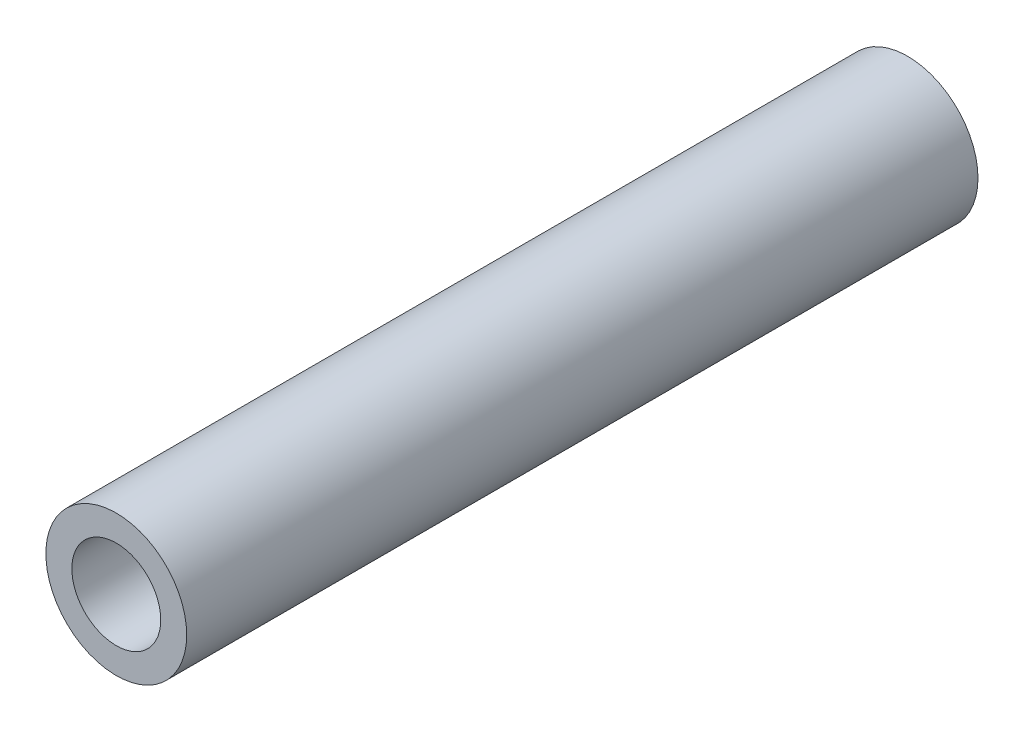
SolidWorks part; units mm, degrees
ref_plane "Front Plane" through (0, 0, 0) normal (0, 0, 1) x (1, 0, 0)
ref_plane "Top Plane" through (0, 0, 0) normal (0, 1, 0) x (1, 0, 0)
ref_plane "Right Plane" through (0, 0, 0) normal (1, 0, 0) x (0, 0, -1)
sketch "Sketch1" plane through (0, 0, 0) normal (0, 0, 1) x (1, 0, 0)
  circle A0 centre (0, 0) radius 3.425
  circle A1 centre (0, 0) radius 5.425
  dimension "D1" = 6.85
  dimension "D2" = 2
extrude "Boss-Extrude1" add sketch "Sketch1" along normal blind 60.96
